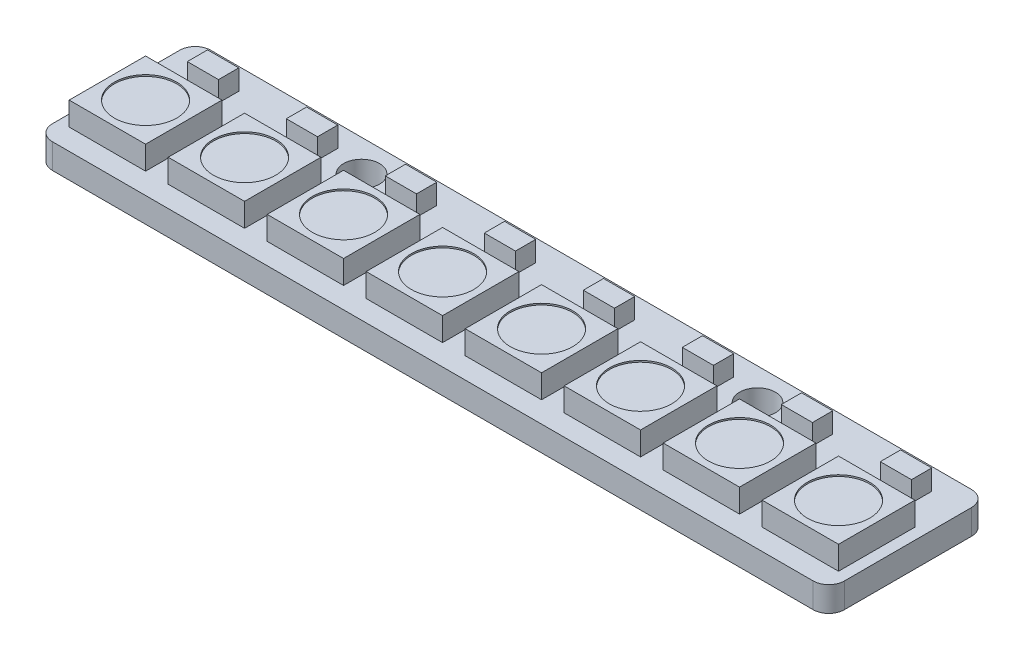
SolidWorks part; units mm, degrees
ref_plane "Front Plane" through (0, 0, 0) normal (0, 0, 1) x (1, 0, 0)
ref_plane "Top Plane" through (0, 0, 0) normal (0, 1, 0) x (1, 0, 0)
ref_plane "Right Plane" through (0, 0, 0) normal (1, 0, 0) x (0, 0, -1)
sketch "Sketch1" plane through (0, 0, 0) normal (0, 1, 0) x (1, 0, 0)
  line L0 (0, 5.08) -> (0, -5.08) construction
  line L1 (-25.4, 5.08) -> (25.4, 5.08)
  line L2 (-25.4, 5.08) -> (-25.4, -5.08)
  line L3 (-25.4, -5.08) -> (25.4, -5.08)
  line L4 (25.4, 5.08) -> (25.4, -5.08)
  line L5 (-25.4, 5.08) -> (25.4, -5.08) construction
  line L6 (-25.4, -5.08) -> (25.4, 5.08) construction
  circle A0 centre (-12.7, 3.048) radius 1.15
  circle A1 centre (12.7, 3.048) radius 1.15
  point P0 (0, 0)
  dimension "D5" = 2.3
  dimension "D1" = 50.8
  dimension "D2" = 10.16
  dimension "D3" = 8.128
  dimension "D4" = 12.7
extrude "PCB" add sketch "Sketch1" along normal blind 1.6
sketch "Sketch2" plane through (0, 1.6, 0) normal (0, 1, 0) x (1, 0, 0)
  line L0 (0, 5.08) -> (0, -5.08) construction
  line L1 (25.4, 5.08) -> (-25.4, 5.08) construction
  line L2 (-25.4, -5.08) -> (25.4, -5.08) construction
  line L3 (-25.4, -1.28) -> (25.4, -1.28) construction
  line L4 (-25.4, 5.08) -> (-25.4, -5.08) construction
  line L5 (25.4, -5.08) -> (25.4, 5.08) construction
  line L6 (0.725, -3.73) -> (5.625, -3.73)
  line L7 (-5.625, 1.17) -> (-0.725, 1.17)
  line L8 (-5.625, 1.17) -> (-5.625, -3.73)
  line L9 (-5.625, -3.73) -> (-0.725, -3.73)
  line L10 (-0.725, 1.17) -> (-0.725, -3.73)
  line L11 (-5.625, 1.17) -> (-0.725, -3.73) construction
  line L12 (-5.625, -3.73) -> (-0.725, 1.17) construction
  line L13 (5.625, 1.17) -> (5.625, -3.73)
  line L14 (0.725, 1.17) -> (5.625, 1.17)
  line L15 (0.725, 1.17) -> (0.725, -3.73)
  line L16 (7.075, -3.73) -> (11.975, -3.73)
  line L17 (11.975, 1.17) -> (11.975, -3.73)
  line L18 (7.075, 1.17) -> (11.975, 1.17)
  line L19 (7.075, 1.17) -> (7.075, -3.73)
  line L20 (13.425, -3.73) -> (18.325, -3.73)
  line L21 (18.325, 1.17) -> (18.325, -3.73)
  line L22 (13.425, 1.17) -> (18.325, 1.17)
  line L23 (13.425, 1.17) -> (13.425, -3.73)
  line L24 (19.775, -3.73) -> (24.675, -3.73)
  line L25 (24.675, 1.17) -> (24.675, -3.73)
  line L26 (19.775, 1.17) -> (24.675, 1.17)
  line L27 (19.775, 1.17) -> (19.775, -3.73)
  line L28 (-19.775, 1.17) -> (-19.775, -3.73)
  line L29 (-19.775, 1.17) -> (-24.675, 1.17)
  line L30 (-24.675, 1.17) -> (-24.675, -3.73)
  line L31 (-19.775, -3.73) -> (-24.675, -3.73)
  line L32 (-13.425, 1.17) -> (-13.425, -3.73)
  line L33 (-13.425, 1.17) -> (-18.325, 1.17)
  line L34 (-18.325, 1.17) -> (-18.325, -3.73)
  line L35 (-13.425, -3.73) -> (-18.325, -3.73)
  line L36 (-7.075, 1.17) -> (-7.075, -3.73)
  line L37 (-7.075, 1.17) -> (-11.975, 1.17)
  line L38 (-11.975, 1.17) -> (-11.975, -3.73)
  line L39 (-7.075, -3.73) -> (-11.975, -3.73)
  point P12 (-3.175, -1.28)
  dimension "D1" = 3.8
  dimension "D2" = 4.9
  dimension "D3" = 6.35
  dimension "D5" = 6.35
  dimension "D4" = 5
extrude "LEDs" add sketch "Sketch2" along normal blind 1.5
sketch "Sketch3" plane through (0, 1.6, 0) normal (0, 1, 0) x (1, 0, 0)
  line L0 (-25.4, 3.048) -> (25.4, 3.048) construction
  line L1 (-25.4, 5.08) -> (-25.4, -5.08) construction
  line L2 (25.4, -5.08) -> (25.4, 5.08) construction
  line L3 (-13.85, 3.048) -> (-11.55, 3.048) construction
  line L4 (-16.875, 3.698) -> (-16.875, 2.398)
  line L5 (-23.225, 3.698) -> (-21.225, 3.698)
  line L6 (-23.225, 3.698) -> (-23.225, 2.398)
  line L7 (-23.225, 2.398) -> (-21.225, 2.398)
  line L8 (-21.225, 3.698) -> (-21.225, 2.398)
  line L9 (-23.225, 3.698) -> (-21.225, 2.398) construction
  line L10 (-23.225, 2.398) -> (-21.225, 3.698) construction
  line L11 (-16.875, 2.398) -> (-14.875, 2.398)
  line L12 (-14.875, 3.698) -> (-14.875, 2.398)
  line L13 (-16.875, 3.698) -> (-14.875, 3.698)
  line L14 (-10.525, 3.698) -> (-10.525, 2.398)
  line L15 (-10.525, 2.398) -> (-8.525, 2.398)
  line L16 (-8.525, 3.698) -> (-8.525, 2.398)
  line L17 (-10.525, 3.698) -> (-8.525, 3.698)
  line L18 (-4.175, 3.698) -> (-4.175, 2.398)
  line L19 (-4.175, 2.398) -> (-2.175, 2.398)
  line L20 (-2.175, 3.698) -> (-2.175, 2.398)
  line L21 (-4.175, 3.698) -> (-2.175, 3.698)
  line L22 (2.175, 3.698) -> (2.175, 2.398)
  line L23 (2.175, 2.398) -> (4.175, 2.398)
  line L24 (4.175, 3.698) -> (4.175, 2.398)
  line L25 (2.175, 3.698) -> (4.175, 3.698)
  line L26 (8.525, 3.698) -> (8.525, 2.398)
  line L27 (8.525, 2.398) -> (10.525, 2.398)
  line L28 (10.525, 3.698) -> (10.525, 2.398)
  line L29 (8.525, 3.698) -> (10.525, 3.698)
  line L30 (14.875, 3.698) -> (14.875, 2.398)
  line L31 (14.875, 2.398) -> (16.875, 2.398)
  line L32 (16.875, 3.698) -> (16.875, 2.398)
  line L33 (14.875, 3.698) -> (16.875, 3.698)
  line L34 (21.225, 3.698) -> (21.225, 2.398)
  line L35 (21.225, 2.398) -> (23.225, 2.398)
  line L36 (23.225, 3.698) -> (23.225, 2.398)
  line L37 (21.225, 3.698) -> (23.225, 3.698)
  line L38 (-24.675, 1.17) -> (-18.325, 1.17) construction
  line L39 (-23.225, 3.698) -> (-16.875, 3.698) construction
  line L40 (-22.225, -3.73) -> (-22.225, 1.17) construction
  line L41 (-24.675, -3.73) -> (-19.775, -3.73) construction
  circle A0 centre (-12.7, 3.048) radius 1.15 construction
  point P11 (-22.225, 3.048)
  dimension "D1" = 2
  dimension "D2" = 1.3
  dimension "D3" = 8
extrude "Caps" add sketch "Sketch3" along normal blind 1.3
sketch "Sketch4" plane through (0, 3.1, 0) normal (0, 1, 0) x (1, 0, 0)
  line L0 (-24.675, 1.17) -> (-19.775, -3.73) construction
  circle A0 centre (-22.225, -1.28) radius 2
  circle A1 centre (-15.875, -1.28) radius 2
  circle A2 centre (-9.525, -1.28) radius 2
  circle A3 centre (-3.175, -1.28) radius 2
  circle A4 centre (3.175, -1.28) radius 2
  circle A5 centre (9.525, -1.28) radius 2
  circle A6 centre (15.875, -1.28) radius 2
  circle A7 centre (22.225, -1.28) radius 2
  dimension "D1" = 4
  dimension "D3" = 6.35
  dimension "D2" = 8
extrude "LED windows" cut sketch "Sketch4" against normal blind 0.1
fillet "Filed fillets" radius 1 4 edges at (-25.4, 0.8, -5.08) (25.4, 0.8, -5.08) (25.4, 0.8, 5.08) (-25.4, 0.8, 5.08)
